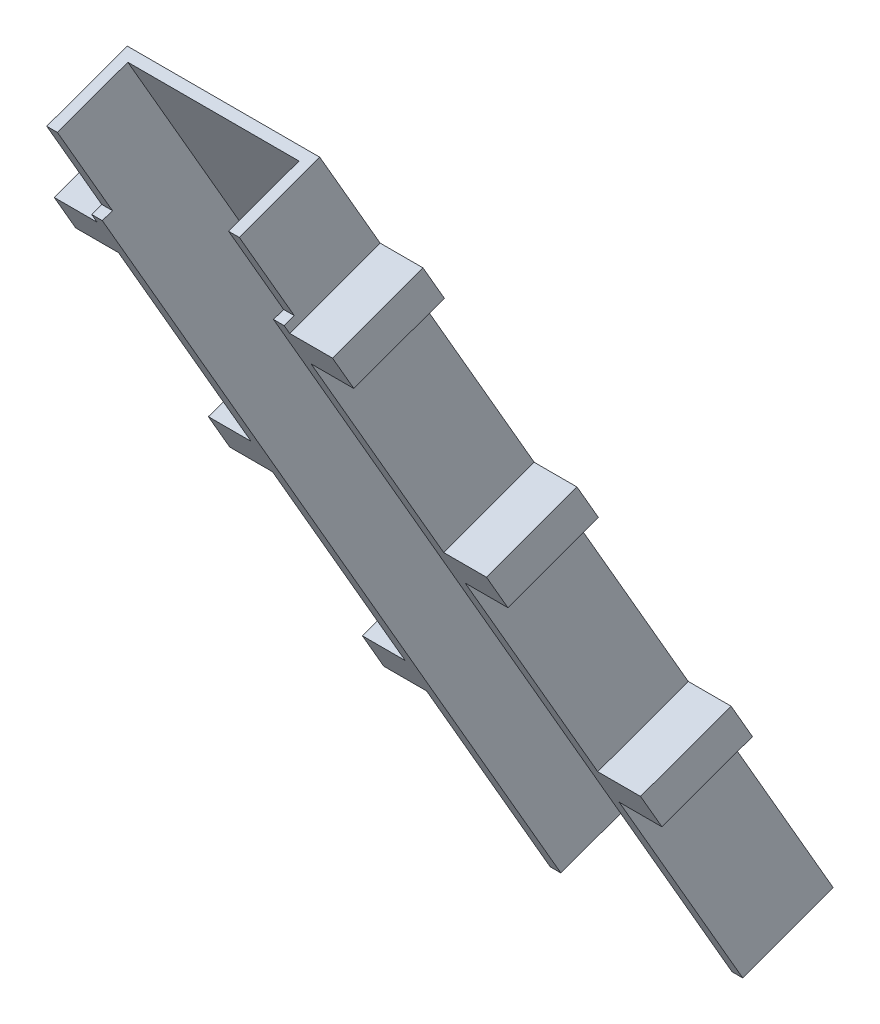
SolidWorks part; units mm, degrees
ref_plane "Front Plane" through (0, 0, 0) normal (0, 0, 1) x (1, 0, 0)
ref_plane "Top Plane" through (0, 0, 0) normal (0, 1, 0) x (1, 0, 0)
ref_plane "Right Plane" through (0, 0, 0) normal (1, 0, 0) x (0, 0, -1)
sketch "Sketch1" plane through (0, 0, 0) normal (1, 0, 0) x (0, 0, -1)
  line L0 (0, 0) -> (-76.2, 131.9823)
  line L1 (-76.2, 131.9823) -> (-59.7906, 137.9548)
  line L2 (-59.7906, 137.9548) -> (16.4094, 5.9725)
  line L4 (0, 0) -> (0, 50000) construction
  line L5 (16.4094, 5.9725) -> (0, 0)
  dimension "D1" = 80
  dimension "D2" = 30
  dimension "D3" = 17.4625
  dimension "D4" = 152.4
extrude "Boss-Extrude1" add sketch "Sketch1" along normal blind 28.575
sketch "Sketch2" plane through (0, 141.0335, 51.332) normal (0, 0.9397, 0.342) x (1, 0, 0)
  line L0 (28.575, -9.0015) -> (0, -9.0015) construction
  line L1 (1.5875, -10.589) -> (26.9875, -10.589)
  line L2 (1.5875, -10.589) -> (1.5875, -24.8765)
  line L3 (1.5875, -24.8765) -> (26.9875, -24.8765)
  line L4 (26.9875, -10.589) -> (26.9875, -24.8765)
  line L5 (28.575, -26.464) -> (0, -26.464) construction
  line L6 (0, -9.0015) -> (0, -26.464) construction
  line L7 (28.575, -9.0015) -> (28.575, -26.464) construction
  dimension "D1" = 1.5875
  dimension "D2" = 1.5875
  dimension "D3" = 1.5875
  dimension "D4" = 1.5875
extrude "Cut-Extrude2" cut sketch "Sketch2" along direction (0, 0.866, 0.5) on the side against the normal through all
sketch "Sketch3" plane through (28.575, 0, 0) normal (1, 0, 0) x (0, 0, -1)
  line L0 (-76.2, 131.9823) -> (-74.7082, 132.5252)
  line L1 (-59.7906, 137.9548) -> (-76.2, 131.9823) construction
  line L2 (-74.7082, 132.5252) -> (-33.4332, 61.0348)
  line L3 (-33.4332, 61.0348) -> (-34.925, 60.4919)
  line L4 (-76.2, 131.9823) -> (0, 0) construction
  line L5 (-34.925, 60.4919) -> (-76.2, 131.9823)
  dimension "D1" = 82.55
  dimension "D2" = 1.5875
extrude "Cut-Extrude3" cut sketch "Sketch3" against normal through all
sketch "Sketch4" plane through (1.5875, 0, 0) normal (1, 0, 0) x (0, 0, -1)
  line L0 (-43.162, 69.1982) -> (-23.7045, 52.8714)
  line L1 (-23.7045, 52.8714) -> (-24.7249, 51.6553)
  line L2 (-24.7249, 51.6553) -> (-44.1824, 67.9821)
  line L3 (-43.162, 69.1982) -> (-44.1824, 67.9821)
  line L4 (1.4918, 0.543) -> (-33.4332, 61.0348) construction
  point P3 (-33.4332, 61.0348)
  dimension "D1" = 25.4
  dimension "D2" = 1.5875
  dimension "D3" = 20
extrude "Cut-Extrude4" cut sketch "Sketch4" along normal blind 25.4
sketch "Sketch6" plane through (0, 0.7817, -1.3539) normal (0, -0.5, 0.866) x (1, 0, 0)
  line L0 (28.575, 69.5743) -> (28.575, 152.1243) construction
  line L1 (26.9875, 152.1243) -> (28.575, 152.1243)
  line L2 (26.9875, 152.1243) -> (26.9875, 69.5743)
  line L3 (26.9875, 69.5743) -> (28.575, 69.5743)
  line L4 (28.575, 152.1243) -> (28.575, 69.5743)
  line L5 (26.9875, 69.5743) -> (28.575, 69.5743) construction
  line L6 (1.5875, 69.5743) -> (1.5875, 152.1243) construction
  line L7 (0, 152.1243) -> (1.5875, 152.1243)
  line L8 (0, 152.1243) -> (0, 69.5743)
  line L9 (0, 69.5743) -> (1.5875, 69.5743)
  line L10 (1.5875, 152.1243) -> (1.5875, 69.5743)
  line L11 (0, 69.5743) -> (1.5875, 69.5743) construction
extrude "Boss-Extrude2" add sketch "Sketch6" along direction (0, -0.342, 0.9397) on the side of the normal blind 1.5875
sketch "Sketch7" plane through (28.575, 0, 0) normal (1, 0, 0) x (0, 0, -1)
  line L0 (-76.2, 131.9823) -> (-71.7247, 133.6111)
  line L1 (-59.7906, 137.9548) -> (-76.2, 131.9823) construction
  line L2 (-71.7247, 133.6111) -> (-63.5685, 119.4841)
  line L3 (0, 0) -> (-76.2, 131.9823) construction
  line L4 (-63.5685, 119.4841) -> (-68.0437, 117.8552)
  line L5 (-68.0437, 117.8552) -> (-76.2, 131.9823)
  dimension "D1" = 4.7625
  dimension "D2" = 16.3125
extrude "Cut-Extrude5" cut sketch "Sketch7" against normal through all
sketch "Sketch8" plane through (28.575, 0, 0) normal (1, 0, 0) x (0, 0, -1)
  line L0 (-68.0437, 117.8552) -> (-65.0602, 118.9411)
  line L1 (-68.0437, 117.8552) -> (-63.5685, 119.4841) construction
  line L2 (-65.0602, 118.9411) -> (2.9835, 1.0859)
  line L3 (0, 0) -> (16.4094, 5.9725) construction
  line L4 (2.9835, 1.0859) -> (0, 0)
  line L5 (0, 0) -> (-68.0437, 117.8552)
  dimension "D1" = 3.175
extrude "Cut-Extrude6" cut sketch "Sketch8" against normal through all
sketch "Sketch9" plane through (28.575, 0, 0) normal (1, 0, 0) x (0, 0, -1)
  line L0 (-64.2542, 117.5451) -> (-50.8284, 122.4317)
  line L1 (2.9835, 1.0859) -> (-65.0602, 118.9411) construction
  line L2 (-50.8284, 122.4317) -> (-47.6534, 116.9325)
  line L3 (-47.6534, 116.9325) -> (-61.0792, 112.0459)
  line L4 (-61.0792, 112.0459) -> (-64.2542, 117.5451)
  line L6 (-65.0602, 118.9411) -> (-63.5685, 119.4841) construction
  line L7 (-41.3942, 77.9504) -> (-27.9684, 82.8371)
  line L8 (-38.2192, 72.4512) -> (-41.3942, 77.9504)
  line L9 (-27.9684, 82.8371) -> (-24.7934, 77.3378)
  line L10 (-24.7934, 77.3378) -> (-38.2192, 72.4512)
  line L11 (-18.5342, 38.3558) -> (-5.1084, 43.2424)
  line L12 (-15.3592, 32.8565) -> (-18.5342, 38.3558)
  line L13 (-5.1084, 43.2424) -> (-1.9334, 37.7431)
  line L14 (-1.9334, 37.7431) -> (-15.3592, 32.8565)
  dimension "D1" = 6.35
  dimension "D2" = 1.5875
  dimension "D3" = 14.2875
  dimension "D5" = 45.72
  dimension "D4" = 3
extrude "Boss-Extrude3" add sketch "Sketch9" along normal blind 6.35 separate body
ref_plane "Plane1" through (14.2875, 0, 0) normal (-1, 0, 0) x (0, 0, 1)
mirror "Mirror1" about plane through (14.2875, 0, 0) normal (-1, 0, 0) of bodies 110 111 109
combine bodies "Combine1" operation type add bodies to combine 108 110 111 109 114 113 112
